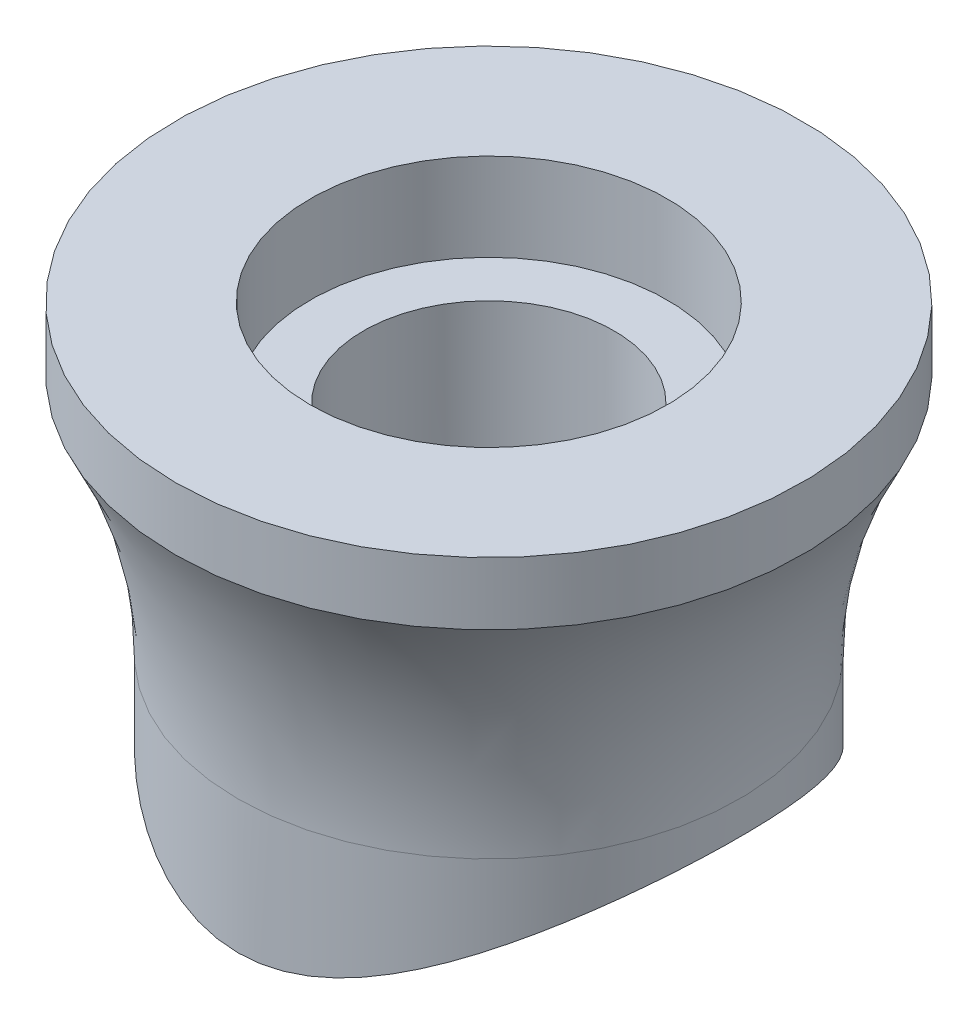
SolidWorks part; units mm, degrees
ref_plane "Plan de face" through (0, 0, 0) normal (0, 0, 1) x (1, 0, 0)
ref_plane "Plan de dessus" through (0, 0, 0) normal (0, 1, 0) x (1, 0, 0)
ref_plane "Plan de droite" through (0, 0, 0) normal (1, 0, 0) x (0, 0, -1)
sketch "Esquisse1" plane through (0, 0, 0) normal (0, 0, 1) x (1, 0, 0)
  line L0 (0, 35.9833) -> (0, -67.207) construction
  line L1 (10, -22) -> (10, -7)
  line L2 (14.25, 0) -> (25, 0)
  line L3 (25, 0) -> (25, -5)
  line L4 (20, -35) -> (20, -24.3649)
  line L5 (19.5, -35) -> (20, -35)
  line L6 (10, -7) -> (14.25, -7)
  line L7 (14.25, -7) -> (14.25, 0)
  line L8 (10, -22) -> (19.5, -35)
  arc A0 (20, -24.3649) -> (25, -5) centre (60, -24.3649) cw
  dimension "D5" = 40
  dimension "D1" = 40
  dimension "D2" = 50
  dimension "D3" = 5
  dimension "D4" = 35
  dimension "D6" = 20
  dimension "D7" = 28.5
  dimension "D8" = 7
  dimension "D9" = 39
  dimension "D10" = 13
revolve "Révolution1" add sketch "Esquisse1" angle 360 about L0
sketch "Esquisse2" plane through (0, 0, 0) normal (1, 0, 0) x (0, 0, -1)
  line L0 (-20, -35) -> (20, -35) construction
  line L1 (20, -35) -> (20, -24.3649) construction
  arc A0 (20, -35) -> (-20, -35) centre (0, -56) ccw
  dimension "D1" = 8
extrude "Enlèv. mat.-Extru.1" cut sketch "Esquisse2" against normal through all and the other way through all
